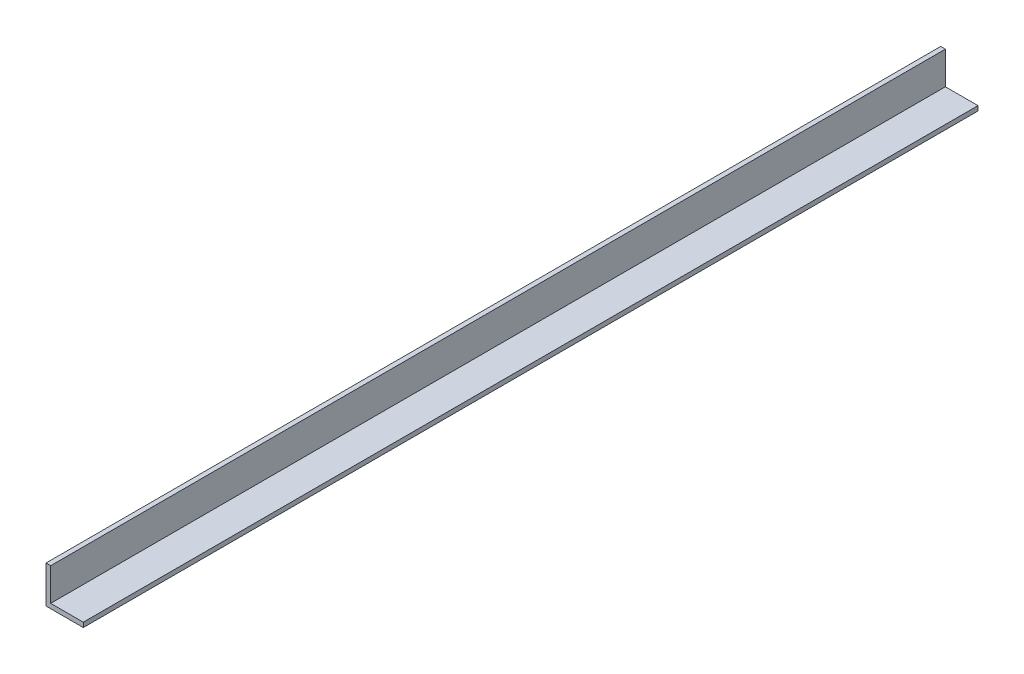
SolidWorks part; units mm, degrees
ref_plane "Front Plane" through (0, 0, 0) normal (0, 0, 1) x (1, 0, 0)
ref_plane "Top Plane" through (0, 0, 0) normal (0, 1, 0) x (1, 0, 0)
ref_plane "Right Plane" through (0, 0, 0) normal (1, 0, 0) x (0, 0, -1)
sketch "Sketch1" plane through (0, 0, 0) normal (0, 0, 1) x (1, 0, 0)
  line L0 (0, 25.4) -> (0, 0)
  line L1 (0, 0) -> (25.4, 0)
  line L2 (25.4, 0) -> (25.4, 3.175)
  line L3 (25.4, 3.175) -> (3.175, 3.175)
  line L4 (3.175, 3.175) -> (3.175, 25.4)
  line L5 (3.175, 25.4) -> (0, 25.4)
  dimension "D1" = 3.175
  dimension "D2" = 25.4
extrude "Boss-Extrude1" add sketch "Sketch1" along normal mid plane 609.6
